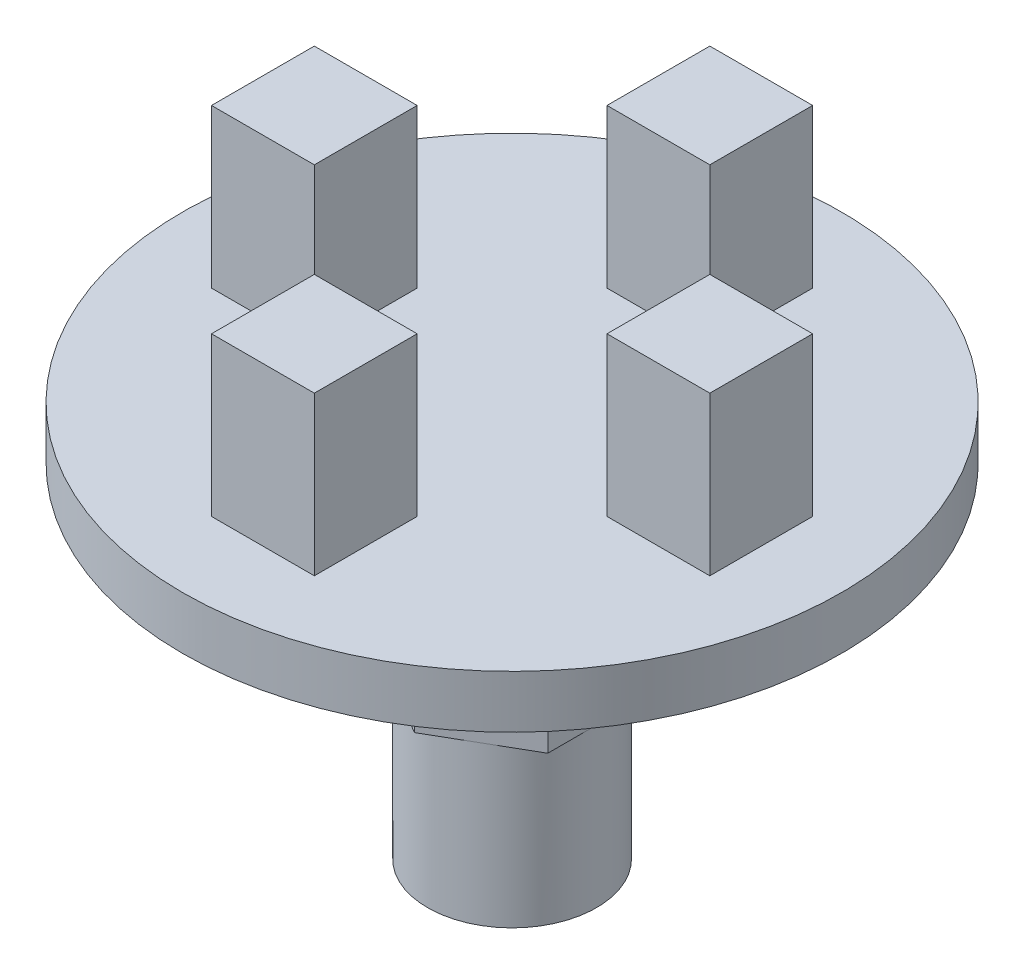
SolidWorks part; units mm, degrees
ref_plane "Front Plane" through (0, 0, 0) normal (0, 0, 1) x (1, 0, 0)
ref_plane "Top Plane" through (0, 0, 0) normal (0, 1, 0) x (1, 0, 0)
ref_plane "Right Plane" through (0, 0, 0) normal (1, 0, 0) x (0, 0, -1)
sketch "Sketch1" plane through (0, 0, 0) normal (0, 1, 0) x (1, 0, 0)
  circle A0 centre (0, 0) radius 12.5
  dimension "D1" = 25
extrude "Boss-Extrude1" add sketch "Sketch1" along normal mid plane 2
sketch "Sketch2" plane through (0, 1, 0) normal (0, 1, 0) x (1, 0, 0)
  line L1 (-2, 9.5) -> (2, 9.5) construction
  line L2 (-2, 9.5) -> (-2, 5.5) construction
  line L3 (-2, 5.5) -> (2, 5.5) construction
  line L4 (2, 9.5) -> (2, 5.5) construction
  line L5 (-1.95, 9.45) -> (-1.95, 5.55)
  line L6 (-1.95, 5.55) -> (1.95, 5.55)
  line L7 (1.95, 9.45) -> (1.95, 5.55)
  line L8 (-1.95, 9.45) -> (1.95, 9.45)
  line L9 (9.45, 1.95) -> (5.55, 1.95)
  line L10 (5.55, 1.95) -> (5.55, -1.95)
  line L11 (9.45, -1.95) -> (5.55, -1.95)
  line L12 (9.45, 1.95) -> (9.45, -1.95)
  line L13 (1.95, -9.45) -> (1.95, -5.55)
  line L14 (1.95, -5.55) -> (-1.95, -5.55)
  line L15 (-1.95, -9.45) -> (-1.95, -5.55)
  line L16 (1.95, -9.45) -> (-1.95, -9.45)
  line L17 (-9.45, -1.95) -> (-5.55, -1.95)
  line L18 (-5.55, -1.95) -> (-5.55, 1.95)
  line L19 (-9.45, 1.95) -> (-5.55, 1.95)
  line L20 (-9.45, -1.95) -> (-9.45, 1.95)
  point P4 (0, 5.5)
  point P25 (0, 0)
  dimension "D1" = 5.5
  dimension "D2" = 4
  dimension "D3" = 4
  dimension "D4" = 0.05
  dimension "D5" = 4
extrude "Boss-Extrude3" add sketch "Sketch2" along normal blind 6
sketch "Sketch3" plane through (0, -1, 0) normal (0, -1, 0) x (1, 0, 0)
  circle A0 centre (0, 0) radius 5
  dimension "D1" = 10
extrude "Boss-Extrude4" add sketch "Sketch3" along normal blind 1
sketch "Sketch4" plane through (0, -2, 0) normal (0, -1, 0) x (1, 0, 0)
  line L1 (0, -3.7) -> (3.2043, -1.85)
  line L2 (3.2043, -1.85) -> (3.2043, 1.85)
  line L3 (3.2043, 1.85) -> (0, 3.7)
  line L4 (0, 3.7) -> (-3.2043, 1.85)
  line L5 (-3.2043, 1.85) -> (-3.2043, -1.85)
  line L6 (-3.2043, -1.85) -> (0, -3.7)
  circle A0 centre (0, 0) radius 3.7 construction
  circle A1 centre (0, 0) radius 3.2043 construction
  dimension "D1" = 7.4
extrude "Boss-Extrude5" add sketch "Sketch4" along normal blind 6
sketch "Sketch5" plane through (0, -8, 0) normal (0, -1, 0) x (-1, 0, 0)
  line L0 (0, 3.7) -> (-3.2043, 1.85) construction
  circle A0 centre (0, 0) radius 3.2043
extrude "Boss-Extrude6" add sketch "Sketch5" along normal blind 6
